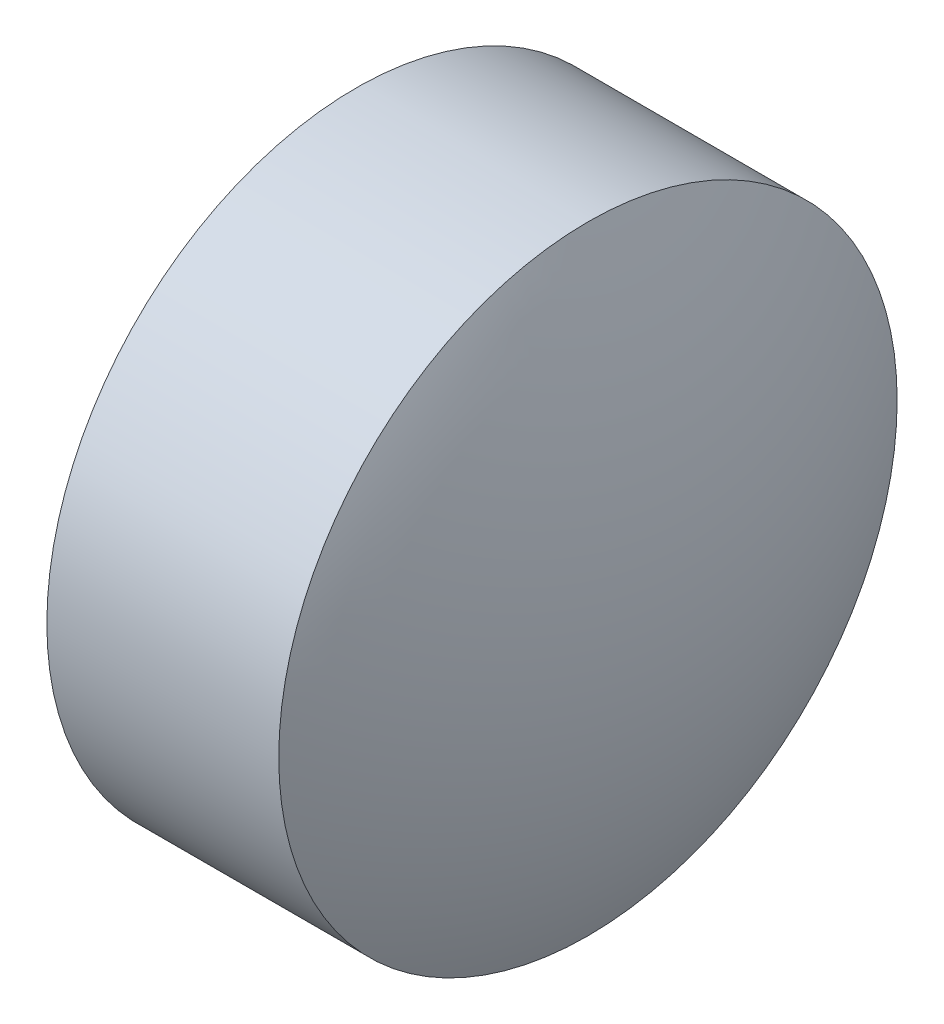
SolidWorks part; units mm, degrees
ref_plane "前视基准面" through (0, 0, 0) normal (0, 0, 1) x (1, 0, 0)
ref_plane "上视基准面" through (0, 0, 0) normal (0, 1, 0) x (1, 0, 0)
ref_plane "右视基准面" through (0, 0, 0) normal (1, 0, 0) x (0, 0, -1)
sketch "草图1" plane through (0, 0, 0) normal (0, 0, 1) x (1, 0, 0)
  line L0 (416.5568, 167.1089) -> (419.2543, 167.1089) construction
  line L1 (416.9849, 167.1089) -> (416.9849, 169.1089)
  line L2 (418.9449, 167.1089) -> (416.9849, 167.1089)
  line L5 (416.9849, 169.1089) -> (418.4849, 169.1089)
  arc A0 (418.9449, 167.1089) -> (418.4849, 169.1089) centre (414.3671, 167.1089) ccw
revolve "旋转1" add sketch "草图1" angle 360 about L0
